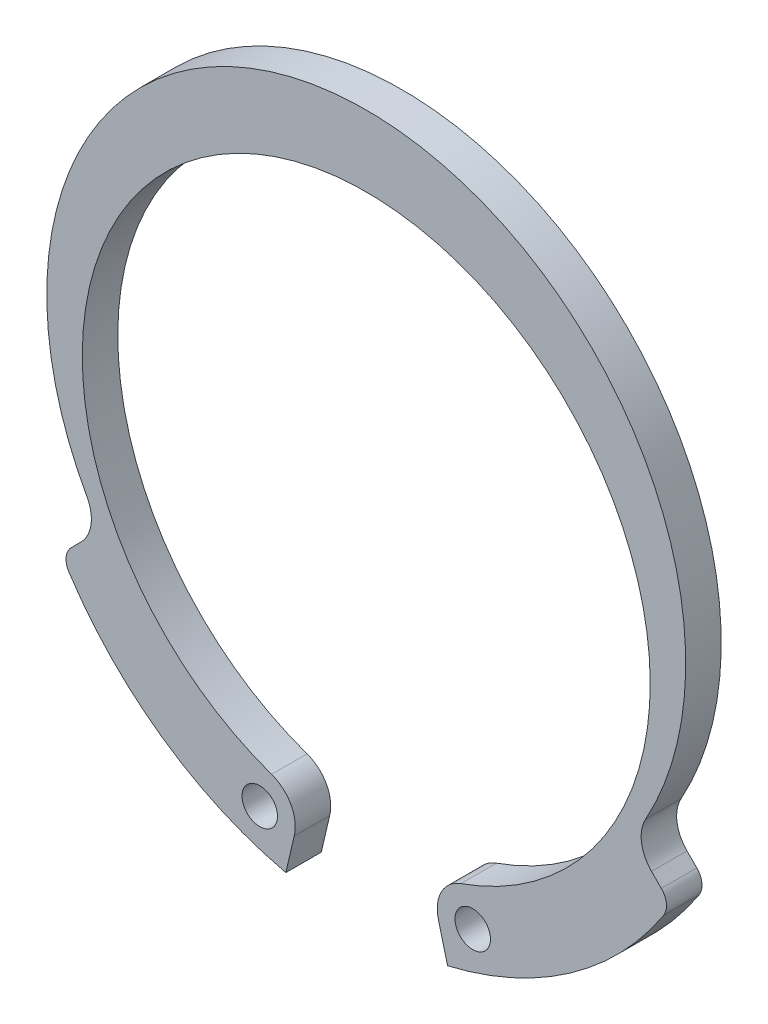
SolidWorks part; units mm, degrees
ref_plane "Front Plane" through (0, 0, 0) normal (0, 0, 1) x (1, 0, 0)
ref_plane "Top Plane" through (0, 0, 0) normal (0, 1, 0) x (1, 0, 0)
ref_plane "Right Plane" through (0, 0, 0) normal (1, 0, 0) x (0, 0, -1)
sketch "Sketch1" plane through (0, 0, 0) normal (0, 0, 1) x (1, 0, 0)
  line L0 (0, 17.6875) -> (0, -17.6875) construction
  line L1 (-2.1964, -10.0804) -> (-2.1121, -10.0804) construction
  line L4 (2.1217, -10.0804) -> (2.1964, -10.0804) construction
  line L5 (-8.0368, -5.5593) -> (-8.3119, -5.8344)
  line L6 (8.0368, -5.5593) -> (8.3119, -5.8344)
  line L7 (-2.0323, -9.7373) -> (-2.2655, -10.74)
  line L8 (2.0323, -9.7373) -> (2.2918, -10.7338)
  arc A0 (7.8695, -4.367) -> (-7.8695, -4.367) centre (0, 0) ccw
  arc A1 (2.6667, -8.5425) -> (-2.6667, -8.5425) centre (0, -1) ccw
  circle A2 centre (-3, -9.4853) radius 0.5
  circle A3 centre (3, -9.4853) radius 0.5
  arc A4 (-8.3772, -6.461) -> (-2.2655, -10.74) centre (0, -1) ccw
  arc A5 (2.6667, -8.5425) -> (2.0323, -9.7373) centre (3, -9.4853) ccw
  arc A6 (-2.0323, -9.7373) -> (-2.6667, -8.5425) centre (-3, -9.4853) ccw
  arc A7 (2.2918, -10.7338) -> (8.3772, -6.461) centre (0, -1) ccw
  arc A8 (-8.0368, -5.5593) -> (-7.8695, -4.367) centre (-8.7439, -4.8522) ccw
  arc A9 (-8.3119, -5.8344) -> (-8.3772, -6.461) centre (-7.9583, -6.188) ccw
  arc A10 (8.3119, -5.8344) -> (8.3772, -6.461) centre (7.9583, -6.188) cw
  arc A11 (8.0368, -5.5593) -> (7.8695, -4.367) centre (8.7439, -4.8522) cw
  point P8 (0, 0)
  point P11 (0, -10.0804)
  point P12 (-7.481, -5.0035)
  point P29 (-8.5927, -6.1152)
  point P33 (8.5927, -6.1152)
  point P36 (7.481, -5.0035)
  dimension "D1" = 18
  dimension "D2" = 16
  dimension "D4" = 1
  dimension "D5" = 1
  dimension "D9" = 20
  dimension "D10" = 2
  dimension "D11" = 1
  dimension "D12" = 2
  dimension "D3" = 1
  dimension "D13" = 0.5
  dimension "D14" = 0.5
  dimension "D15" = 1
  dimension "D6" = 6
  dimension "D7" = 1
  dimension "D8" = 3
extrude "Boss-Extrude1" add sketch "Sketch1" along normal blind 1
